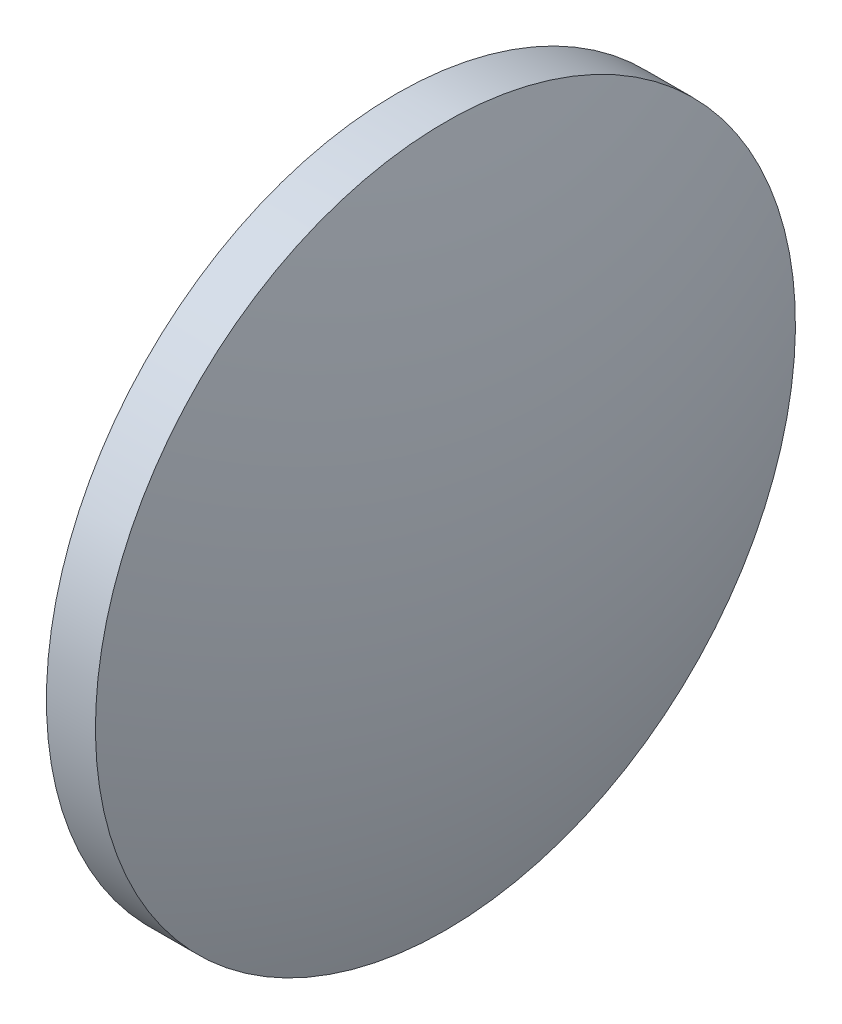
SolidWorks part; units mm, degrees
ref_plane "前视基准面" through (0, 0, 0) normal (0, 0, 1) x (1, 0, 0)
ref_plane "上视基准面" through (0, 0, 0) normal (0, 1, 0) x (1, 0, 0)
ref_plane "右视基准面" through (0, 0, 0) normal (1, 0, 0) x (0, 0, -1)
sketch "草图1" plane through (0, 0, 0) normal (0, 0, 1) x (1, 0, 0)
  line L0 (43.2897, 31.0202) -> (44.1897, 31.0202)
  line L1 (44.1897, 31.0202) -> (44.1897, 18.1702)
  line L2 (44.1897, 18.1702) -> (43.2897, 18.1702)
  line L3 (43.2897, 18.1702) -> (43.2897, 31.0202)
  line L4 (41.0551, 24.5952) -> (46.5103, 24.5952) construction
  arc A0 (43.2897, 31.0202) -> (43.2897, 18.1702) centre (62.4222, 24.5952) ccw
  arc A1 (44.1897, 18.1702) -> (44.1897, 31.0202) centre (25.0573, 24.5952) ccw
  dimension "D1" = 0.9
  dimension "D2" = 12.85
revolve "旋转1" add sketch "草图1" angle 360 about L4
